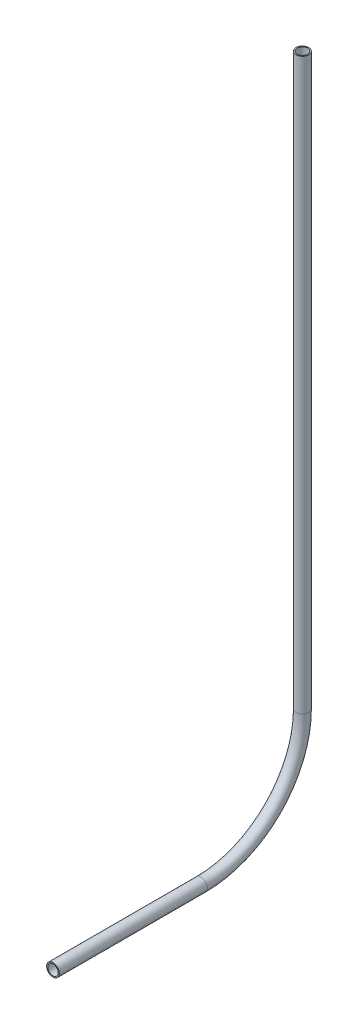
SolidWorks part; units mm, degrees
ref_plane "Front Plane" through (0, 0, 0) normal (0, 0, 1) x (1, 0, 0)
ref_plane "Top Plane" through (0, 0, 0) normal (0, 1, 0) x (1, 0, 0)
ref_plane "Right Plane" through (0, 0, 0) normal (1, 0, 0) x (0, 0, -1)
sketch "Sketch1" plane through (0, 0, 0) normal (1, 0, 0) x (0, 0, -1)
  line L0 (-132.1046, 164.6839) -> (-57.921, 164.6839)
  line L1 (-7.121, 215.4839) -> (-7.121, 500.8232)
  arc A0 (-57.921, 164.6839) -> (-7.121, 215.4839) centre (-57.921, 215.4839) ccw
  point P2 (-132.1046, 164.6839)
  dimension "D1" = 50.8
other "Pipe 0.5 SCH 40(1)"
ref_plane "Plane1" through (0, 164.6839, 132.1046) normal (0, 0, -1) x (0, 1, 0)
sketch "Sketch11" plane through (0, 164.6839, 132.1046) normal (0, 0, -1) x (0, 1, 0)
  circle A0 centre (0, 0) radius 3.175
  circle A1 centre (0, 0) radius 2.6162
  point P5 (0, 0)
  dimension "In_dia" = 6.35
  dimension "Out_dia" = 5.2324
